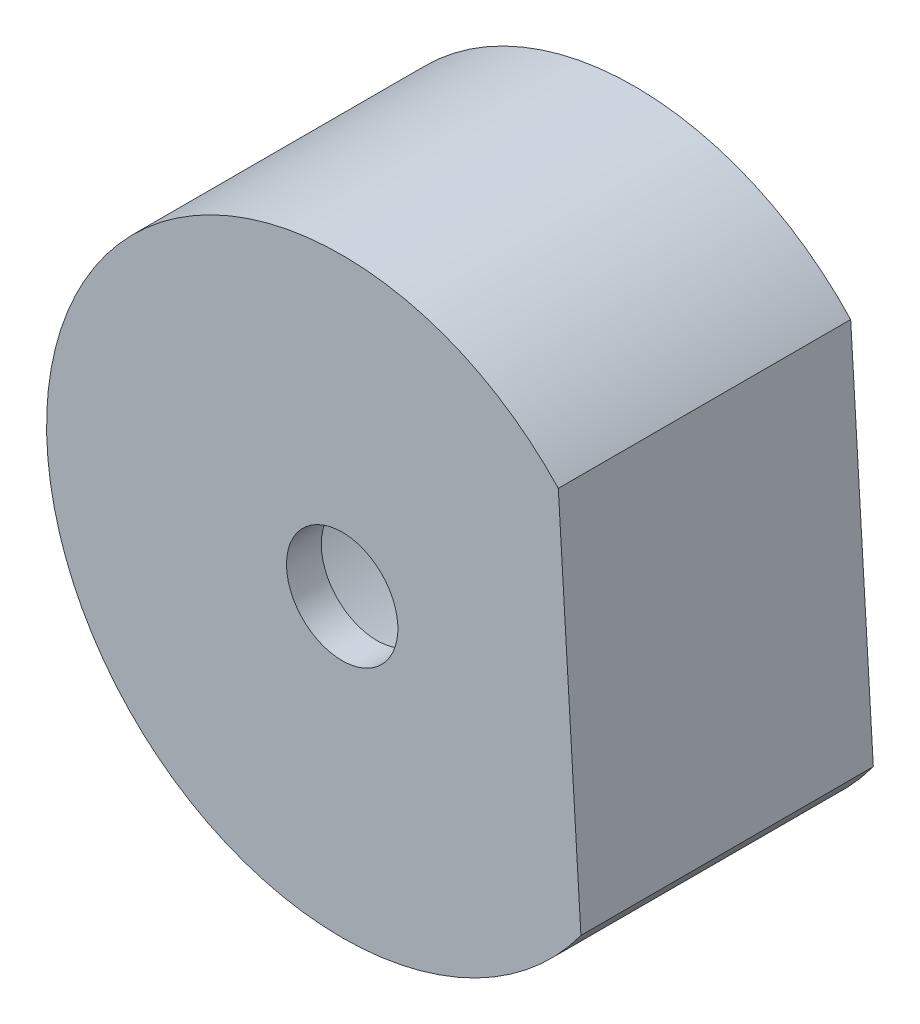
SolidWorks part; units mm, degrees
ref_plane "Front Plane" through (0, 0, 0) normal (0, 0, 1) x (1, 0, 0)
ref_plane "Top Plane" through (0, 0, 0) normal (0, 1, 0) x (1, 0, 0)
ref_plane "Right Plane" through (0, 0, 0) normal (1, 0, 0) x (0, 0, -1)
sketch "Sketch1" plane through (0, 0, 0) normal (0, 0, 1) x (1, 0, 0)
  circle A1 centre (78.5762, -343.707) radius 5.992
  circle A2 centre (78.5762, -343.707) radius 8.492
  dimension "D1" = 2.5
extrude "Boss-Extrude1" add sketch "Sketch1" along normal blind 7.4
sketch "Sketch2" plane through (0, 0, 7.4) normal (0, 0, 1) x (1, 0, 0)
  circle A0 centre (78.5762, -343.707) radius 8.492 construction
  circle A1 centre (78.5762, -343.707) radius 8.492
extrude "Boss-Extrude2" add sketch "Sketch2" along normal blind 1
sketch "Sketch3" plane through (0, 0, 0) normal (0, 0, -1) x (-1, 0, 0)
  line L2 (-84.7853, -337.9138) -> (-85.4356, -348.7133)
  circle A1 centre (-78.5762, -343.707) radius 8.492 construction
  arc A2 (-84.7853, -337.9138) -> (-85.4356, -348.7133) centre (-78.5762, -343.707) ccw
extrude "Cut-Extrude1" cut sketch "Sketch3" against normal blind 18.3
hole_wizard "M3 Clearance Hole1" positions "Sketch5" profile "Sketch4" hole size "M3" standard "ISO" end condition through all
sketch "Sketch5" plane through (0, 0, 7.4) normal (0, 0, -1) x (-1, 0, 0)
  point P0 (-78.5762, -343.707)
sketch "Sketch4" plane through (78.5762, -343.707, 7.4) normal (1, 0, 0) x (0, 1, 0)
  line L0 (0, 0) -> (0, 1)
  line L1 (0, 1) -> (1.6, 1)
  line L2 (1.6, 1) -> (1.6, 0)
  line L5 (1.6, 0) -> (0, 0)
  line L11 (0, -6.35) -> (0, 107.95) construction
  dimension "Thru Hole Dia." = 3.2
  dimension "Thru Hole Depth" = 1
